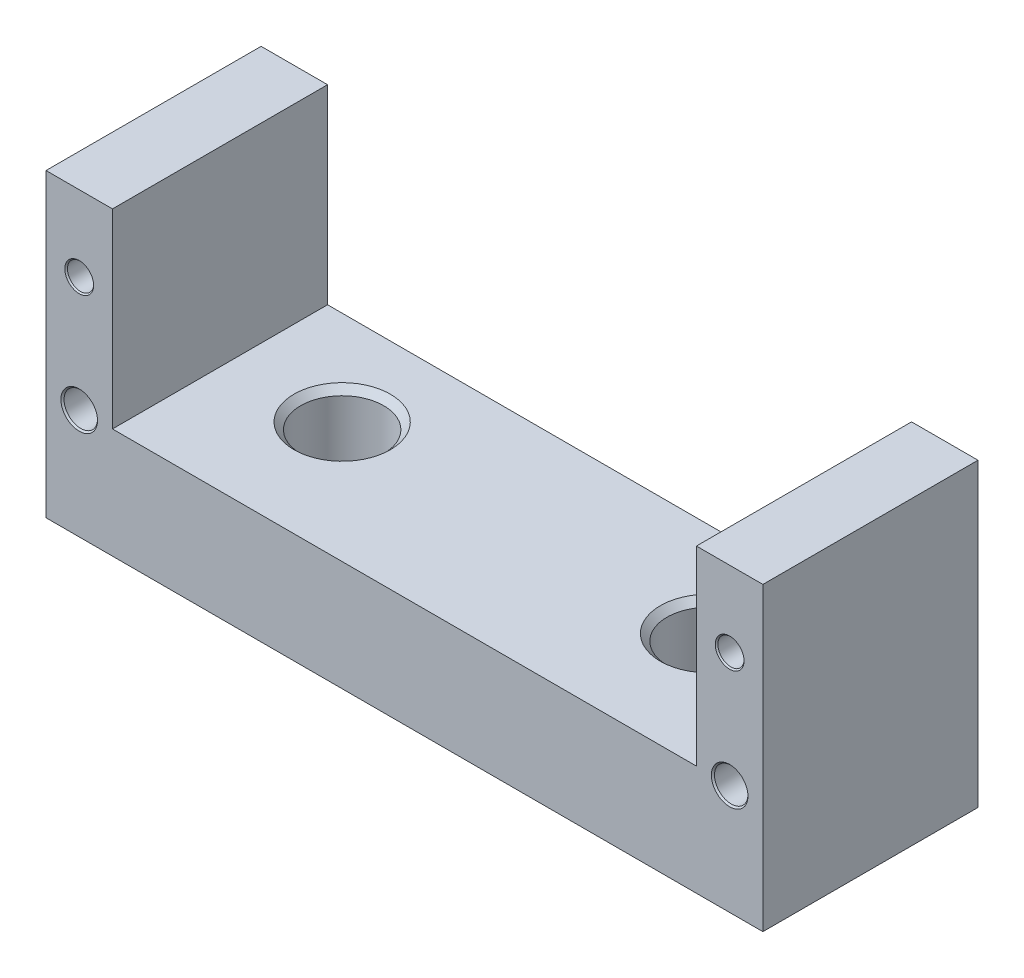
SolidWorks part; units mm, degrees
ref_plane "Front Plane" through (0, 0, 0) normal (0, 0, 1) x (1, 0, 0)
ref_plane "Top Plane" through (0, 0, 0) normal (0, 1, 0) x (1, 0, 0)
ref_plane "Right Plane" through (0, 0, 0) normal (1, 0, 0) x (0, 0, -1)
sketch "Sketch1" plane through (0, 0, 0) normal (0, 1, 0) x (1, 0, 0)
  line L1 (-34.2436, 20.55) -> (34.2436, 20.55)
  line L2 (-34.2436, 20.55) -> (-34.2436, 0)
  line L3 (-34.2436, 0) -> (34.2436, 0)
  line L4 (34.2436, 20.55) -> (34.2436, 0)
  dimension "D1" = 20.55
  dimension "D2" = 68.4872
extrude "Boss-Extrude1" add sketch "Sketch1" along normal blind 28.732
sketch "Sketch2" plane through (0, 0, 0) normal (0, 0, 1) x (1, 0, 0)
  line L0 (-34.2436, 28.732) -> (34.2436, 28.732) construction
  line L1 (-27.8936, 28.732) -> (27.8936, 28.732)
  line L2 (-27.8936, 28.732) -> (-27.8936, 10.525)
  line L3 (-27.8936, 10.525) -> (27.8936, 10.525)
  line L4 (27.8936, 28.732) -> (27.8936, 10.525)
  line L5 (0, 0) -> (0, 10.525) construction
  dimension "D1" = 18.207
  dimension "D2" = 55.7872
extrude "Cut-Extrude1" cut sketch "Sketch2" against normal through all
hole_wizard "Ø2.5 (2.5) Diameter Hole1" positions "Sketch4" profile "Sketch5" hole size "Ø2.5" standard "Ansi Metric" end condition through all
sketch "Sketch4" plane through (0, 0, 0) normal (0, 0, 1) x (1, 0, 0)
  line L0 (-31.0686, 21.5) -> (31.0686, 21.5) construction
  line L1 (0, 0) -> (0, 21.5) construction
  line L2 (-34.2436, 0) -> (34.2436, 0) construction
  point P0 (-31.0686, 21.5)
  point P1 (31.0686, 21.5)
  dimension "D1" = 21.5
  dimension "D2" = 62.1372
sketch "Sketch5" plane through (-31.0686, 21.5, 0) normal (1, 0, 0) x (0, -1, 0)
  line L0 (0, 0) -> (0, 20.55)
  line L1 (0, 20.55) -> (1.375, 20.55)
  line L2 (1.25, 20.425) -> (1.25, 0.125)
  line L3 (1.25, 0.125) -> (1.375, 0)
  line L5 (1.375, 0) -> (0, 0)
  line L6 (-1.25, 0.125) -> (-1.375, 0) construction
  line L7 (1.375, 20.55) -> (1.25, 20.425)
  line L8 (-1.375, 20.55) -> (-1.25, 20.425) construction
  line L11 (0, -6.35) -> (0, 107.95) construction
  dimension "Thru Hole Dia." = 2.5
  dimension "Thru Hole Depth" = 20.55
  dimension "Near C'Sink Dia." = 2.75
  dimension "Near C'Sink Angle" = 90
  dimension "Far C'Sink Dia." = 2.75
  dimension "Far C'Sink Angle" = 90
hole_wizard "Ø3.2 (3.2) Diameter Hole1" positions "Sketch7" profile "Sketch8" hole size "Ø3.2" standard "Ansi Metric" end condition through all
sketch "Sketch7" plane through (0, 0, 0) normal (0, 0, 1) x (1, 0, 0)
  line L0 (-31.0686, 21.5) -> (-31.0686, 10.5) construction
  line L1 (31.0686, 21.5) -> (31.0686, 10.5) construction
  line L2 (-34.2436, 0) -> (34.2436, 0) construction
  point P0 (-31.0686, 10.5)
  point P1 (31.0686, 10.5)
  dimension "D1" = 10.5
sketch "Sketch8" plane through (-31.0686, 10.5, 0) normal (1, 0, 0) x (0, -1, 0)
  line L0 (0, 0) -> (0, 20.55)
  line L1 (0, 20.55) -> (1.75, 20.55)
  line L2 (1.6, 20.4) -> (1.6, 0.15)
  line L3 (1.6, 0.15) -> (1.75, 0)
  line L5 (1.75, 0) -> (0, 0)
  line L6 (-1.6, 0.15) -> (-1.75, 0) construction
  line L7 (1.75, 20.55) -> (1.6, 20.4)
  line L8 (-1.75, 20.55) -> (-1.6, 20.4) construction
  line L11 (0, -6.35) -> (0, 107.95) construction
  dimension "Thru Hole Dia." = 3.2
  dimension "Thru Hole Depth" = 20.55
  dimension "Near C'Sink Dia." = 3.5
  dimension "Near C'Sink Angle" = 90
  dimension "Far C'Sink Dia." = 3.5
  dimension "Far C'Sink Angle" = 90
hole_wizard "5/16 (0.3125) Diameter Hole1" positions "Sketch10" profile "Sketch11" hole size "5/16" standard "Ansi Inch" end condition through all
sketch "Sketch10" plane through (0, 10.525, 0) normal (0, 1, 0) x (-1, 0, 0)
  line L0 (17.5, -11.55) -> (-17.5, -11.55) construction
  line L1 (0, 0) -> (0, -11.55) construction
  line L2 (27.8936, 0) -> (-27.8936, 0) construction
  line L4 (27.8936, -20.55) -> (-27.8936, -20.55) construction
  point P0 (17.5, -11.55)
  point P1 (-17.5, -11.55)
  dimension "D1" = 9
  dimension "D2" = 35
sketch "Sketch11" plane through (-17.5, 10.525, -11.55) normal (1, 0, 0) x (0, 0, 1)
  line L0 (0, 0) -> (0, 10.525)
  line L1 (0, 10.525) -> (3.9687, 10.525)
  line L2 (3.9687, 10.525) -> (3.9687, 0.635)
  line L3 (3.9687, 0.635) -> (4.6037, 0)
  line L5 (4.6037, 0) -> (0, 0)
  line L6 (-3.9687, 0.635) -> (-4.6037, 0) construction
  line L11 (0, -6.35) -> (0, 107.95) construction
  dimension "Thru Hole Dia." = 7.9375
  dimension "Thru Hole Depth" = 10.525
  dimension "Near C'Sink Dia." = 9.2075
  dimension "Near C'Sink Angle" = 90
hole_wizard "1/8 (0.125) Diameter Hole1" positions "Sketch13" profile "Sketch14" hole size "1/8" standard "Ansi Inch"
sketch "Sketch13" plane through (0, 0, 0) normal (0, -1, 0) x (1, 0, 0)
  line L0 (27.5, -11.55) -> (-27.5, -11.55) construction
  line L1 (0, -20.55) -> (0, -11.55) construction
  line L2 (34.2436, -20.55) -> (-34.2436, -20.55) construction
  point P0 (27.5, -11.55)
  point P1 (-27.5, -11.55)
  dimension "D1" = 55
  dimension "D2" = 9
sketch "Sketch14" plane through (27.5, 0, -11.55) normal (1, 0, 0) x (0, 0, -1)
  line L0 (0, 0) -> (0, 10.4839)
  line L1 (0, 10.4839) -> (1.5875, 9.53)
  line L2 (1.5875, 9.53) -> (1.5875, 0.3175)
  line L3 (1.5875, 0.3175) -> (1.905, 0)
  line L5 (1.905, 0) -> (0, 0)
  line L6 (-1.5875, 0.3175) -> (-1.905, 0) construction
  line L10 (0, 10.4839) -> (-1.5875, 9.53) construction
  line L11 (0, -6.35) -> (0, 107.95) construction
  dimension "Hole Dia." = 3.175
  dimension "Hole Depth" = 9.53
  dimension "Near C'Sink Dia." = 3.81
  dimension "Near C'Sink Angle" = 90
  dimension "Drill Angle" = 118
